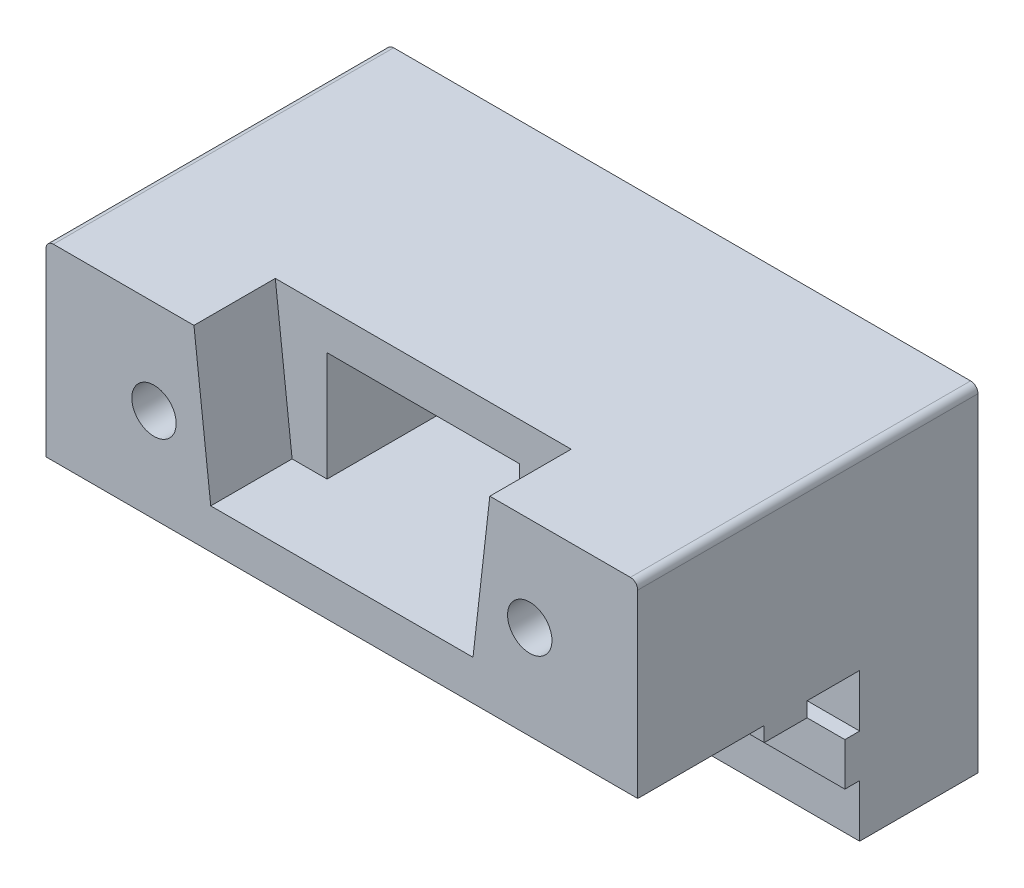
SolidWorks part; units mm, degrees
ref_plane "Front Plane" through (0, 0, 0) normal (0, 0, 1) x (1, 0, 0)
ref_plane "Top Plane" through (0, 0, 0) normal (0, 1, 0) x (1, 0, 0)
ref_plane "Right Plane" through (0, 0, 0) normal (1, 0, 0) x (0, 0, -1)
sketch "Esquisse1" plane through (0, 0, 0) normal (0, 0, 1) x (1, 0, 0)
  line L1 (-20, 6.35) -> (20, 6.35)
  line L2 (-20, 6.35) -> (-20, -6.35)
  line L3 (-20, -6.35) -> (20, -6.35)
  line L4 (20, 6.35) -> (20, -6.35)
  point P4 (0, 6.35)
  point P6 (-20, 0)
  dimension "D1" = 40
  dimension "D2" = 12.7
extrude "Boss.-Extru.1" add sketch "Esquisse1" along normal blind 23
ref_plane "Plan End of DSub" through (0, 0, 17.5) normal (0, 0, 1) x (1, 0, 0)
fillet "Congé1" radius 0.5 2 edges at (20, 6.35, 11.5) (-20, 6.35, 11.5)
sketch "Esquisse2" plane through (0, 0, 23) normal (0, 0, 1) x (1, 0, 0)
  circle A0 centre (-12.7, 0) radius 1.5
  circle A1 centre (12.7, 0) radius 1.5
  point P4 (0, 0)
  dimension "D1" = 3
  dimension "D2" = 25.4
  dimension "D3" = 12.7
extrude "Enlèv. mat.-Extru.1" cut sketch "Esquisse2" against normal through all
sketch "Esquisse4" plane through (0, 0, 23) normal (0, 0, -1) x (-1, 0, 0)
  line L0 (-10, 6.35) -> (10, 6.35)
  line L1 (10, 6.35) -> (8.5, -6.85)
  line L2 (8.5, -6.85) -> (-8.5, -6.85)
  line L3 (-8.5, -6.85) -> (-10, 6.35)
  line L4 (-20, -6.35) -> (-20, 5.85) construction
  line L5 (-19.5, 6.35) -> (19.5, 6.35) construction
  point P4 (-20, -0.25)
  point P7 (-9.25, -0.25)
  point P8 (0, 6.35)
  point P11 (0, 6.35)
  dimension "D1" = 20
  dimension "D2" = 17
extrude "Enlèv. mat.-Extru.2" cut sketch "Esquisse4" against normal up to surface (5.5 mm away)
sketch "Esquisse5" plane through (0, 0, 17.5) normal (0, 0, 1) x (1, 0, 0)
  line L0 (-10, 6.35) -> (10, 6.35) construction
  line L1 (-6.5, 3.75) -> (6.5, 3.75)
  line L2 (-6.5, 3.75) -> (-6.5, -4.25)
  line L3 (-6.5, -4.25) -> (6.5, -4.25)
  line L4 (6.5, 3.75) -> (6.5, -4.25)
  line L5 (20, -6.35) -> (20, 5.85) construction
  point P4 (0, 3.75)
  point P7 (0, 6.35)
  point P10 (20, -0.25)
  point P11 (-6.5, -0.25)
  dimension "D1" = 8
  dimension "D2" = 13
extrude "Enlèv. mat.-Extru.3" cut sketch "Esquisse5" against normal through all
ref_plane "Plan1" through (0, -3.65, 0) normal (0, -1, 0) x (-1, 0, 0)
sketch "Esquisse17" plane through (-20, 0, 0) normal (-1, 0, 0) x (0, 0, 1)
  line L0 (8, -16.35) -> (0, -16.35)
  line L1 (0, -16.35) -> (0, -3.65)
  line L2 (0, 5.85) -> (0, -6.35) construction
  line L3 (0, -3.65) -> (23, -3.65)
  line L4 (23, -3.65) -> (23, -6.35)
  line L5 (23, -6.35) -> (14.45, -6.35)
  line L6 (14.45, -6.35) -> (14.45, -7.35)
  line L7 (14.45, -7.35) -> (11.55, -7.35)
  line L8 (11.55, -7.35) -> (11.55, -6.35)
  line L9 (11.55, -6.35) -> (8, -6.35)
  line L10 (8, -6.35) -> (8, -9.9)
  line L11 (8, -9.9) -> (9, -9.9)
  line L12 (9, -9.9) -> (9, -12.8)
  line L13 (9, -12.8) -> (8, -12.8)
  line L14 (8, -12.8) -> (8, -16.35)
  line L15 (23, -6.35) -> (0, -6.35) construction
  line L16 (-12.65, -3.65) -> (12.65, -3.65) construction
  line L17 (23, 5.85) -> (23, -6.35) construction
  dimension "D1" = 2.9
  dimension "D2" = 3.55
  dimension "D3" = 8
  dimension "D4" = 1
extrude "Boss.-Extru.8" add sketch "Esquisse17" against normal up to surface (40 mm away) up to face at (20, -0.25, 11.5)
sketch "Esquisse16" plane through (0, 0, 0) normal (0, 0, -1) x (-1, 0, 0)
  circle A0 centre (-12.7, 0) radius 4
  circle A1 centre (12.7, 0) radius 4
  dimension "D1" = 8
extrude "Enlèv. mat.-Extru.10" cut sketch "Esquisse16" against normal blind 13
sketch "Esquisse18" plane through (0, 0, 0) normal (0, 0, -1) x (-1, 0, 0)
  line L0 (-20, -16.35) -> (20, -16.35) construction
  circle A0 centre (0, -11.35) radius 4
  point P5 (0, -16.35)
  dimension "D2" = 8
  dimension "D1" = 5
extrude "Enlèv. mat.-Extru.11" cut sketch "Esquisse18" against normal blind 5
sketch "Esquisse19" plane through (0, 0, 5) normal (0, 0, -1) x (-1, 0, 0)
  circle A0 centre (0, -11.35) radius 1.5
  circle A1 centre (0, -11.35) radius 4 construction
  dimension "D1" = 3
extrude "Enlèv. mat.-Extru.12" cut sketch "Esquisse19" against normal through all
